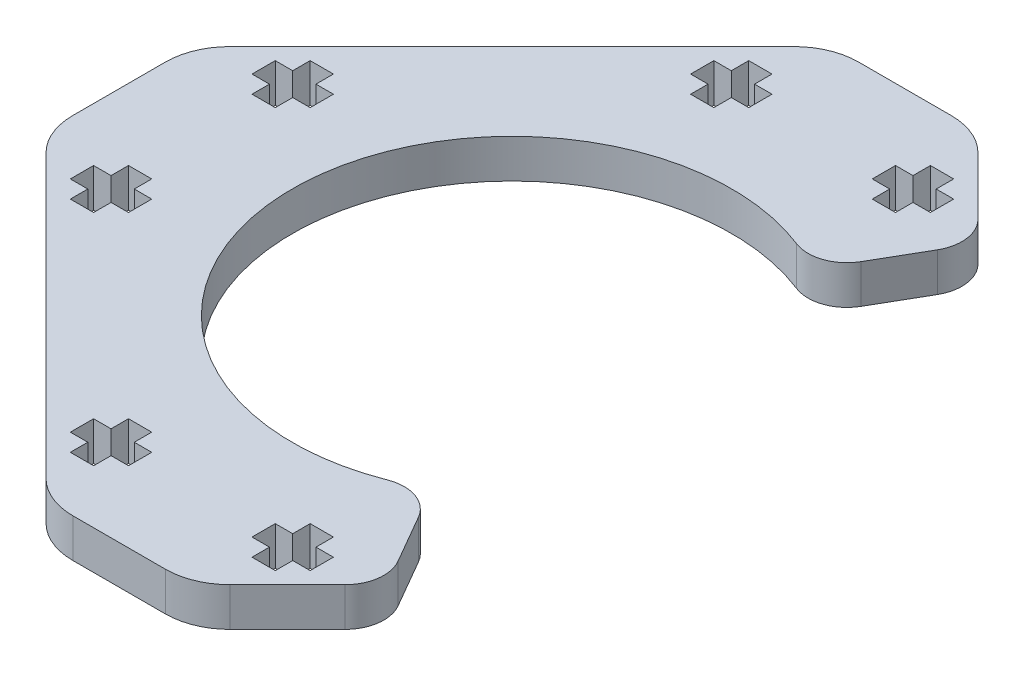
SolidWorks part; units mm, degrees
ref_plane "Front Plane" through (0, 0, 0) normal (0, 0, 1) x (1, 0, 0)
ref_plane "Top Plane" through (0, 0, 0) normal (0, 1, 0) x (1, 0, 0)
ref_plane "Right Plane" through (0, 0, 0) normal (1, 0, 0) x (0, 0, -1)
sketch "Sketch1" plane through (0, 0, 0) normal (0, 1, 0) x (1, 0, 0)
  line L0 (17.5699, 22.8627) -> (11.4915, 28.9411)
  line L1 (7.956, 30.4056) -> (0.7844, 30.4056)
  line L2 (-2.7512, 28.9411) -> (-24.571, 7.1213)
  line L3 (-26.0354, 3.5858) -> (-26.0354, -3.5858)
  line L4 (-24.571, -7.1213) -> (-2.7512, -28.9411)
  line L5 (0.7844, -30.4056) -> (7.956, -30.4056)
  line L6 (11.4915, -28.9411) -> (17.5699, -22.8627)
  line L11 (-11.5989, 5.83) -> (4.3702, 0) construction
  line L12 (-11.5989, -5.83) -> (4.3702, 0) construction
  line L13 (-3.7616, 22.2739) -> (4.3702, 0) construction
  line L14 (12.8702, 14.7224) -> (17.5699, 22.8627)
  line L15 (12.8702, -14.7224) -> (17.5699, -22.8627)
  arc A7 (11.4915, 28.9411) -> (7.956, 30.4056) centre (7.956, 25.4056) ccw
  arc A8 (0.7844, 30.4056) -> (-2.7512, 28.9411) centre (0.7844, 25.4056) ccw
  arc A9 (-24.571, 7.1213) -> (-26.0354, 3.5858) centre (-21.0354, 3.5858) ccw
  arc A10 (-26.0354, -3.5858) -> (-24.571, -7.1213) centre (-21.0354, -3.5858) ccw
  arc A11 (-2.7512, -28.9411) -> (0.7844, -30.4056) centre (0.7844, -25.4056) ccw
  arc A12 (7.956, -30.4056) -> (11.4915, -28.9411) centre (7.956, -25.4056) ccw
  arc A16 (12.8702, 14.7224) -> (12.8702, -14.7224) centre (4.3702, 0) ccw
  dimension "D1" = 51
  dimension "D2" = 17
extrude "Boss-Extrude1" add sketch "Sketch1" along normal blind 3
sketch "Sketch2" plane through (0, 3, 0) normal (0, 1, 0) x (1, 0, 0)
  line L12 (-21.8798, 7.9294) -> (-21.8798, 6.1294)
  line L13 (-21.8798, 6.1294) -> (-20.5298, 6.1294)
  line L14 (-20.5298, 6.1294) -> (-20.5298, 4.7794)
  line L15 (-20.5298, 4.7794) -> (-18.7298, 4.7794)
  line L16 (-18.7298, 4.7794) -> (-18.7298, 6.1294)
  line L17 (-18.7298, 6.1294) -> (-17.3798, 6.1294)
  line L18 (-17.3798, 6.1294) -> (-17.3798, 7.9294)
  line L19 (-17.3798, 7.9294) -> (-18.7298, 7.9294)
  line L20 (-18.7298, 7.9294) -> (-18.7298, 9.2794)
  line L21 (-18.7298, 9.2794) -> (-20.5298, 9.2794)
  line L22 (-20.5298, 9.2794) -> (-20.5298, 7.9294)
  line L23 (-20.5298, 7.9294) -> (-21.8798, 7.9294)
  line L24 (-21.8798, 7.9294) -> (-21.8798, 6.1294)
  line L25 (-21.8798, 6.1294) -> (-20.5298, 6.1294)
  line L26 (-20.5298, 6.1294) -> (-20.5298, 4.7794)
  line L27 (-20.5298, 4.7794) -> (-18.7298, 4.7794)
  line L28 (-18.7298, 4.7794) -> (-18.7298, 6.1294)
  line L29 (-18.7298, 6.1294) -> (-17.3798, 6.1294)
  line L30 (-17.3798, 6.1294) -> (-17.3798, 7.9294)
  line L31 (-17.3798, 7.9294) -> (-18.7298, 7.9294)
  line L32 (-18.7298, 7.9294) -> (-18.7298, 9.2794)
  line L33 (-18.7298, 9.2794) -> (-20.5298, 9.2794)
  line L34 (-20.5298, 9.2794) -> (-20.5298, 7.9294)
  line L35 (-20.5298, 7.9294) -> (-21.8798, 7.9294)
  line L36 (-18.7298, -4.7794) -> (-20.5298, -4.7794)
  line L37 (-20.5298, -4.7794) -> (-20.5298, -6.1294)
  line L38 (-20.5298, -6.1294) -> (-21.8798, -6.1294)
  line L39 (-21.8798, -6.1294) -> (-21.8798, -7.9294)
  line L40 (-21.8798, -7.9294) -> (-20.5298, -7.9294)
  line L41 (-20.5298, -7.9294) -> (-20.5298, -9.2794)
  line L42 (-20.5298, -9.2794) -> (-18.7298, -9.2794)
  line L43 (-18.7298, -9.2794) -> (-18.7298, -7.9294)
  line L44 (-18.7298, -7.9294) -> (-17.3798, -7.9294)
  line L45 (-17.3798, -7.9294) -> (-17.3798, -6.1294)
  line L46 (-17.3798, -6.1294) -> (-18.7298, -6.1294)
  line L47 (-18.7298, -6.1294) -> (-18.7298, -4.7794)
  line L48 (-18.7298, -4.7794) -> (-20.5298, -4.7794)
  line L49 (-20.5298, -4.7794) -> (-20.5298, -6.1294)
  line L50 (-20.5298, -6.1294) -> (-21.8798, -6.1294)
  line L51 (-21.8798, -6.1294) -> (-21.8798, -7.9294)
  line L52 (-21.8798, -7.9294) -> (-20.5298, -7.9294)
  line L53 (-20.5298, -7.9294) -> (-20.5298, -9.2794)
  line L54 (-20.5298, -9.2794) -> (-18.7298, -9.2794)
  line L55 (-18.7298, -9.2794) -> (-18.7298, -7.9294)
  line L56 (-18.7298, -7.9294) -> (-17.3798, -7.9294)
  line L57 (-17.3798, -7.9294) -> (-17.3798, -6.1294)
  line L58 (-17.3798, -6.1294) -> (-18.7298, -6.1294)
  line L59 (-18.7298, -6.1294) -> (-18.7298, -4.7794)
  line L60 (12.2996, 23.1) -> (13.6496, 23.1)
  line L61 (13.6496, 23.1) -> (13.6496, 24.9)
  line L62 (13.6496, 24.9) -> (12.2996, 24.9)
  line L63 (12.2996, 24.9) -> (12.2996, 26.25)
  line L64 (12.2996, 26.25) -> (10.4996, 26.25)
  line L65 (10.4996, 26.25) -> (10.4996, 24.9)
  line L66 (10.4996, 24.9) -> (9.1496, 24.9)
  line L67 (9.1496, 24.9) -> (9.1496, 23.1)
  line L68 (9.1496, 23.1) -> (10.4996, 23.1)
  line L69 (10.4996, 23.1) -> (10.4996, 21.75)
  line L70 (10.4996, 21.75) -> (12.2996, 21.75)
  line L71 (12.2996, 21.75) -> (12.2996, 23.1)
  line L72 (12.2996, 23.1) -> (13.6496, 23.1)
  line L73 (13.6496, 23.1) -> (13.6496, 24.9)
  line L74 (13.6496, 24.9) -> (12.2996, 24.9)
  line L75 (12.2996, 24.9) -> (12.2996, 26.25)
  line L76 (12.2996, 26.25) -> (10.4996, 26.25)
  line L77 (10.4996, 26.25) -> (10.4996, 24.9)
  line L78 (10.4996, 24.9) -> (9.1496, 24.9)
  line L79 (9.1496, 24.9) -> (9.1496, 23.1)
  line L80 (9.1496, 23.1) -> (10.4996, 23.1)
  line L81 (10.4996, 23.1) -> (10.4996, 21.75)
  line L82 (10.4996, 21.75) -> (12.2996, 21.75)
  line L83 (12.2996, 21.75) -> (12.2996, 23.1)
  line L84 (30.6202, -7.9294) -> (30.6202, -6.1294)
  line L85 (30.6202, -6.1294) -> (29.2702, -6.1294)
  line L86 (29.2702, -6.1294) -> (29.2702, -4.7794)
  line L87 (29.2702, -4.7794) -> (27.4702, -4.7794)
  line L88 (27.4702, -4.7794) -> (27.4702, -6.1294)
  line L89 (27.4702, -6.1294) -> (26.1202, -6.1294)
  line L90 (26.1202, -6.1294) -> (26.1202, -7.9294)
  line L91 (26.1202, -7.9294) -> (27.4702, -7.9294)
  line L92 (27.4702, -7.9294) -> (27.4702, -9.2794)
  line L93 (27.4702, -9.2794) -> (29.2702, -9.2794)
  line L94 (29.2702, -9.2794) -> (29.2702, -7.9294)
  line L95 (29.2702, -7.9294) -> (30.6202, -7.9294)
  line L96 (30.6202, -7.9294) -> (30.6202, -6.1294)
  line L97 (30.6202, -6.1294) -> (29.2702, -6.1294)
  line L98 (29.2702, -6.1294) -> (29.2702, -4.7794)
  line L99 (29.2702, -4.7794) -> (27.4702, -4.7794)
  line L100 (27.4702, -4.7794) -> (27.4702, -6.1294)
  line L101 (27.4702, -6.1294) -> (26.1202, -6.1294)
  line L102 (26.1202, -6.1294) -> (26.1202, -7.9294)
  line L103 (26.1202, -7.9294) -> (27.4702, -7.9294)
  line L104 (27.4702, -7.9294) -> (27.4702, -9.2794)
  line L105 (27.4702, -9.2794) -> (29.2702, -9.2794)
  line L106 (29.2702, -9.2794) -> (29.2702, -7.9294)
  line L107 (29.2702, -7.9294) -> (30.6202, -7.9294)
  line L108 (-0.4093, 24.9) -> (-1.7593, 24.9)
  line L109 (-1.7593, 24.9) -> (-1.7593, 26.25)
  line L110 (-1.7593, 26.25) -> (-3.5593, 26.25)
  line L111 (-3.5593, 26.25) -> (-3.5593, 24.9)
  line L112 (-3.5593, 24.9) -> (-4.9093, 24.9)
  line L113 (-4.9093, 24.9) -> (-4.9093, 23.1)
  line L114 (-4.9093, 23.1) -> (-3.5593, 23.1)
  line L115 (-3.5593, 23.1) -> (-3.5593, 21.75)
  line L116 (-3.5593, 21.75) -> (-1.7593, 21.75)
  line L117 (-1.7593, 21.75) -> (-1.7593, 23.1)
  line L118 (-1.7593, 23.1) -> (-0.4093, 23.1)
  line L119 (-0.4093, 23.1) -> (-0.4093, 24.9)
  line L120 (-0.4093, 24.9) -> (-1.7593, 24.9)
  line L121 (-1.7593, 24.9) -> (-1.7593, 26.25)
  line L122 (-1.7593, 26.25) -> (-3.5593, 26.25)
  line L123 (-3.5593, 26.25) -> (-3.5593, 24.9)
  line L124 (-3.5593, 24.9) -> (-4.9093, 24.9)
  line L125 (-4.9093, 24.9) -> (-4.9093, 23.1)
  line L126 (-4.9093, 23.1) -> (-3.5593, 23.1)
  line L127 (-3.5593, 23.1) -> (-3.5593, 21.75)
  line L128 (-3.5593, 21.75) -> (-1.7593, 21.75)
  line L129 (-1.7593, 21.75) -> (-1.7593, 23.1)
  line L130 (-1.7593, 23.1) -> (-0.4093, 23.1)
  line L131 (-0.4093, 23.1) -> (-0.4093, 24.9)
  line L132 (30.6202, 7.9294) -> (29.2702, 7.9294)
  line L133 (30.6202, 6.1294) -> (30.6202, 7.9294)
  line L134 (29.2702, 6.1294) -> (30.6202, 6.1294)
  line L135 (29.2702, 4.7794) -> (29.2702, 6.1294)
  line L136 (27.4702, 4.7794) -> (29.2702, 4.7794)
  line L137 (27.4702, 6.1294) -> (27.4702, 4.7794)
  line L138 (26.1202, 6.1294) -> (27.4702, 6.1294)
  line L139 (26.1202, 7.9294) -> (26.1202, 6.1294)
  line L140 (27.4702, 7.9294) -> (26.1202, 7.9294)
  line L141 (27.4702, 9.2794) -> (27.4702, 7.9294)
  line L142 (29.2702, 9.2794) -> (27.4702, 9.2794)
  line L143 (29.2702, 7.9294) -> (29.2702, 9.2794)
  line L144 (30.6202, 7.9294) -> (29.2702, 7.9294)
  line L145 (30.6202, 6.1294) -> (30.6202, 7.9294)
  line L146 (29.2702, 6.1294) -> (30.6202, 6.1294)
  line L147 (29.2702, 4.7794) -> (29.2702, 6.1294)
  line L148 (27.4702, 4.7794) -> (29.2702, 4.7794)
  line L149 (27.4702, 6.1294) -> (27.4702, 4.7794)
  line L150 (26.1202, 6.1294) -> (27.4702, 6.1294)
  line L151 (26.1202, 7.9294) -> (26.1202, 6.1294)
  line L152 (27.4702, 7.9294) -> (26.1202, 7.9294)
  line L153 (27.4702, 9.2794) -> (27.4702, 7.9294)
  line L154 (29.2702, 9.2794) -> (27.4702, 9.2794)
  line L155 (29.2702, 7.9294) -> (29.2702, 9.2794)
  line L156 (-1.7593, -26.25) -> (-1.7593, -24.9)
  line L157 (-1.7593, -24.9) -> (-0.4093, -24.9)
  line L158 (-0.4093, -24.9) -> (-0.4093, -23.1)
  line L159 (-0.4093, -23.1) -> (-1.7593, -23.1)
  line L160 (-1.7593, -23.1) -> (-1.7593, -21.75)
  line L161 (-1.7593, -21.75) -> (-3.5593, -21.75)
  line L162 (-3.5593, -21.75) -> (-3.5593, -23.1)
  line L163 (-3.5593, -23.1) -> (-4.9093, -23.1)
  line L164 (-4.9093, -23.1) -> (-4.9093, -24.9)
  line L165 (-4.9093, -24.9) -> (-3.5593, -24.9)
  line L166 (-3.5593, -24.9) -> (-3.5593, -26.25)
  line L167 (-3.5593, -26.25) -> (-1.7593, -26.25)
  line L168 (-1.7593, -26.25) -> (-1.7593, -24.9)
  line L169 (-1.7593, -24.9) -> (-0.4093, -24.9)
  line L170 (-0.4093, -24.9) -> (-0.4093, -23.1)
  line L171 (-0.4093, -23.1) -> (-1.7593, -23.1)
  line L172 (-1.7593, -23.1) -> (-1.7593, -21.75)
  line L173 (-1.7593, -21.75) -> (-3.5593, -21.75)
  line L174 (-3.5593, -21.75) -> (-3.5593, -23.1)
  line L175 (-3.5593, -23.1) -> (-4.9093, -23.1)
  line L176 (-4.9093, -23.1) -> (-4.9093, -24.9)
  line L177 (-4.9093, -24.9) -> (-3.5593, -24.9)
  line L178 (-3.5593, -24.9) -> (-3.5593, -26.25)
  line L179 (-3.5593, -26.25) -> (-1.7593, -26.25)
  line L180 (12.2996, -26.25) -> (12.2996, -24.9)
  line L181 (12.2996, -24.9) -> (13.6496, -24.9)
  line L182 (13.6496, -24.9) -> (13.6496, -23.1)
  line L183 (13.6496, -23.1) -> (12.2996, -23.1)
  line L184 (12.2996, -23.1) -> (12.2996, -21.75)
  line L185 (12.2996, -21.75) -> (10.4996, -21.75)
  line L186 (10.4996, -21.75) -> (10.4996, -23.1)
  line L187 (10.4996, -23.1) -> (9.1496, -23.1)
  line L188 (9.1496, -23.1) -> (9.1496, -24.9)
  line L189 (9.1496, -24.9) -> (10.4996, -24.9)
  line L190 (10.4996, -24.9) -> (10.4996, -26.25)
  line L191 (10.4996, -26.25) -> (12.2996, -26.25)
  line L192 (12.2996, -26.25) -> (12.2996, -24.9)
  line L193 (12.2996, -24.9) -> (13.6496, -24.9)
  line L194 (13.6496, -24.9) -> (13.6496, -23.1)
  line L195 (13.6496, -23.1) -> (12.2996, -23.1)
  line L196 (12.2996, -23.1) -> (12.2996, -21.75)
  line L197 (12.2996, -21.75) -> (10.4996, -21.75)
  line L198 (10.4996, -21.75) -> (10.4996, -23.1)
  line L199 (10.4996, -23.1) -> (9.1496, -23.1)
  line L200 (9.1496, -23.1) -> (9.1496, -24.9)
  line L201 (9.1496, -24.9) -> (10.4996, -24.9)
  line L202 (10.4996, -24.9) -> (10.4996, -26.25)
  line L203 (10.4996, -26.25) -> (12.2996, -26.25)
  dimension "D1" = 0
  dimension "D2" = 0
  dimension "D3" = 0
  dimension "D4" = 0
  dimension "D5" = 0
  dimension "D6" = 0
  dimension "D7" = 0
  dimension "D8" = 0
extrude "Cut-Extrude1" cut sketch "Sketch2" against normal through all
fillet "Fillet1" radius 3 4 edges at (17.5699, 1.5, 22.8627) (12.8702, 1.5, 14.7224) (17.5699, 1.5, -22.8627) (12.8702, 1.5, -14.7224)
sketch "Sketch3" plane through (0, 3, 0) normal (0, 1, 0) x (1, 0, 0)
  line L9 (11.4915, -28.9411) -> (15.9422, -24.4904)
  line L10 (16.4189, -20.8691) -> (14.257, -17.1245)
  line L11 (14.257, 17.1245) -> (16.4189, 20.8691)
  line L12 (12.2996, -24.9) -> (13.6496, -24.9)
  line L13 (12.2996, -26.25) -> (12.2996, -24.9)
  line L14 (10.4996, -26.25) -> (12.2996, -26.25)
  line L15 (10.4996, -24.9) -> (10.4996, -26.25)
  line L16 (9.1496, -24.9) -> (10.4996, -24.9)
  line L17 (9.1496, -23.1) -> (9.1496, -24.9)
  line L18 (10.4996, -23.1) -> (9.1496, -23.1)
  line L19 (10.4996, -21.75) -> (10.4996, -23.1)
  line L20 (12.2996, -21.75) -> (10.4996, -21.75)
  line L21 (12.2996, -23.1) -> (12.2996, -21.75)
  line L22 (13.6496, -23.1) -> (12.2996, -23.1)
  line L23 (13.6496, -24.9) -> (13.6496, -23.1)
  line L24 (12.2996, -24.9) -> (13.6496, -24.9)
  line L25 (12.2996, -26.25) -> (12.2996, -24.9)
  line L26 (10.4996, -26.25) -> (12.2996, -26.25)
  line L27 (10.4996, -24.9) -> (10.4996, -26.25)
  line L28 (9.1496, -24.9) -> (10.4996, -24.9)
  line L29 (9.1496, -23.1) -> (9.1496, -24.9)
  line L30 (10.4996, -23.1) -> (9.1496, -23.1)
  line L31 (10.4996, -21.75) -> (10.4996, -23.1)
  line L32 (12.2996, -21.75) -> (10.4996, -21.75)
  line L33 (12.2996, -23.1) -> (12.2996, -21.75)
  line L34 (13.6496, -23.1) -> (12.2996, -23.1)
  line L35 (13.6496, -24.9) -> (13.6496, -23.1)
  line L36 (-1.7593, 24.9) -> (-1.7593, 26.25)
  line L37 (-0.4093, 24.9) -> (-1.7593, 24.9)
  line L38 (-0.4093, 23.1) -> (-0.4093, 24.9)
  line L39 (-1.7593, 23.1) -> (-0.4093, 23.1)
  line L40 (-1.7593, 21.75) -> (-1.7593, 23.1)
  line L41 (-3.5593, 21.75) -> (-1.7593, 21.75)
  line L42 (-3.5593, 23.1) -> (-3.5593, 21.75)
  line L43 (-4.9093, 23.1) -> (-3.5593, 23.1)
  line L44 (-4.9093, 24.9) -> (-4.9093, 23.1)
  line L45 (-3.5593, 24.9) -> (-4.9093, 24.9)
  line L46 (-3.5593, 26.25) -> (-3.5593, 24.9)
  line L47 (-1.7593, 26.25) -> (-3.5593, 26.25)
  line L48 (-1.7593, 24.9) -> (-1.7593, 26.25)
  line L49 (-0.4093, 24.9) -> (-1.7593, 24.9)
  line L50 (-0.4093, 23.1) -> (-0.4093, 24.9)
  line L51 (-1.7593, 23.1) -> (-0.4093, 23.1)
  line L52 (-1.7593, 21.75) -> (-1.7593, 23.1)
  line L53 (-3.5593, 21.75) -> (-1.7593, 21.75)
  line L54 (-3.5593, 23.1) -> (-3.5593, 21.75)
  line L55 (-4.9093, 23.1) -> (-3.5593, 23.1)
  line L56 (-4.9093, 24.9) -> (-4.9093, 23.1)
  line L57 (-3.5593, 24.9) -> (-4.9093, 24.9)
  line L58 (-3.5593, 26.25) -> (-3.5593, 24.9)
  line L59 (-1.7593, 26.25) -> (-3.5593, 26.25)
  line L60 (12.2996, 21.75) -> (12.2996, 23.1)
  line L61 (10.4996, 21.75) -> (12.2996, 21.75)
  line L62 (10.4996, 23.1) -> (10.4996, 21.75)
  line L63 (9.1496, 23.1) -> (10.4996, 23.1)
  line L64 (9.1496, 24.9) -> (9.1496, 23.1)
  line L65 (10.4996, 24.9) -> (9.1496, 24.9)
  line L66 (10.4996, 26.25) -> (10.4996, 24.9)
  line L67 (12.2996, 26.25) -> (10.4996, 26.25)
  line L68 (12.2996, 24.9) -> (12.2996, 26.25)
  line L69 (13.6496, 24.9) -> (12.2996, 24.9)
  line L70 (13.6496, 23.1) -> (13.6496, 24.9)
  line L71 (12.2996, 23.1) -> (13.6496, 23.1)
  line L72 (12.2996, 21.75) -> (12.2996, 23.1)
  line L73 (10.4996, 21.75) -> (12.2996, 21.75)
  line L74 (10.4996, 23.1) -> (10.4996, 21.75)
  line L75 (9.1496, 23.1) -> (10.4996, 23.1)
  line L76 (9.1496, 24.9) -> (9.1496, 23.1)
  line L77 (10.4996, 24.9) -> (9.1496, 24.9)
  line L78 (10.4996, 26.25) -> (10.4996, 24.9)
  line L79 (12.2996, 26.25) -> (10.4996, 26.25)
  line L80 (12.2996, 24.9) -> (12.2996, 26.25)
  line L81 (13.6496, 24.9) -> (12.2996, 24.9)
  line L82 (13.6496, 23.1) -> (13.6496, 24.9)
  line L83 (12.2996, 23.1) -> (13.6496, 23.1)
  line L84 (-20.5298, -4.7794) -> (-20.5298, -6.1294)
  line L85 (-18.7298, -4.7794) -> (-20.5298, -4.7794)
  line L86 (-18.7298, -6.1294) -> (-18.7298, -4.7794)
  line L87 (-17.3798, -6.1294) -> (-18.7298, -6.1294)
  line L88 (-17.3798, -7.9294) -> (-17.3798, -6.1294)
  line L89 (-18.7298, -7.9294) -> (-17.3798, -7.9294)
  line L90 (-18.7298, -9.2794) -> (-18.7298, -7.9294)
  line L91 (-20.5298, -9.2794) -> (-18.7298, -9.2794)
  line L92 (-20.5298, -7.9294) -> (-20.5298, -9.2794)
  line L93 (-21.8798, -7.9294) -> (-20.5298, -7.9294)
  line L94 (-21.8798, -6.1294) -> (-21.8798, -7.9294)
  line L95 (-20.5298, -6.1294) -> (-21.8798, -6.1294)
  line L96 (-20.5298, -4.7794) -> (-20.5298, -6.1294)
  line L97 (-18.7298, -4.7794) -> (-20.5298, -4.7794)
  line L98 (-18.7298, -6.1294) -> (-18.7298, -4.7794)
  line L99 (-17.3798, -6.1294) -> (-18.7298, -6.1294)
  line L100 (-17.3798, -7.9294) -> (-17.3798, -6.1294)
  line L101 (-18.7298, -7.9294) -> (-17.3798, -7.9294)
  line L102 (-18.7298, -9.2794) -> (-18.7298, -7.9294)
  line L103 (-20.5298, -9.2794) -> (-18.7298, -9.2794)
  line L104 (-20.5298, -7.9294) -> (-20.5298, -9.2794)
  line L105 (-21.8798, -7.9294) -> (-20.5298, -7.9294)
  line L106 (-21.8798, -6.1294) -> (-21.8798, -7.9294)
  line L107 (-20.5298, -6.1294) -> (-21.8798, -6.1294)
  line L108 (-20.5298, 7.9294) -> (-21.8798, 7.9294)
  line L109 (-20.5298, 9.2794) -> (-20.5298, 7.9294)
  line L110 (-18.7298, 9.2794) -> (-20.5298, 9.2794)
  line L111 (-18.7298, 7.9294) -> (-18.7298, 9.2794)
  line L112 (-17.3798, 7.9294) -> (-18.7298, 7.9294)
  line L113 (-17.3798, 6.1294) -> (-17.3798, 7.9294)
  line L114 (-18.7298, 6.1294) -> (-17.3798, 6.1294)
  line L115 (-18.7298, 4.7794) -> (-18.7298, 6.1294)
  line L116 (-20.5298, 4.7794) -> (-18.7298, 4.7794)
  line L117 (-20.5298, 6.1294) -> (-20.5298, 4.7794)
  line L118 (-21.8798, 6.1294) -> (-20.5298, 6.1294)
  line L119 (-21.8798, 7.9294) -> (-21.8798, 6.1294)
  line L120 (-20.5298, 7.9294) -> (-21.8798, 7.9294)
  line L121 (-20.5298, 9.2794) -> (-20.5298, 7.9294)
  line L122 (-18.7298, 9.2794) -> (-20.5298, 9.2794)
  line L123 (-18.7298, 7.9294) -> (-18.7298, 9.2794)
  line L124 (-17.3798, 7.9294) -> (-18.7298, 7.9294)
  line L125 (-17.3798, 6.1294) -> (-17.3798, 7.9294)
  line L126 (-18.7298, 6.1294) -> (-17.3798, 6.1294)
  line L127 (-18.7298, 4.7794) -> (-18.7298, 6.1294)
  line L128 (-20.5298, 4.7794) -> (-18.7298, 4.7794)
  line L129 (-20.5298, 6.1294) -> (-20.5298, 4.7794)
  line L130 (-21.8798, 6.1294) -> (-20.5298, 6.1294)
  line L131 (-21.8798, 7.9294) -> (-21.8798, 6.1294)
  line L132 (-3.5593, -26.25) -> (-1.7593, -26.25)
  line L133 (-3.5593, -24.9) -> (-3.5593, -26.25)
  line L134 (-4.9093, -24.9) -> (-3.5593, -24.9)
  line L135 (-4.9093, -23.1) -> (-4.9093, -24.9)
  line L136 (-3.5593, -23.1) -> (-4.9093, -23.1)
  line L137 (-3.5593, -21.75) -> (-3.5593, -23.1)
  line L138 (-1.7593, -21.75) -> (-3.5593, -21.75)
  line L139 (-1.7593, -23.1) -> (-1.7593, -21.75)
  line L140 (-0.4093, -23.1) -> (-1.7593, -23.1)
  line L141 (-0.4093, -24.9) -> (-0.4093, -23.1)
  line L142 (-1.7593, -24.9) -> (-0.4093, -24.9)
  line L143 (-1.7593, -26.25) -> (-1.7593, -24.9)
  line L144 (-3.5593, -26.25) -> (-1.7593, -26.25)
  line L145 (-3.5593, -24.9) -> (-3.5593, -26.25)
  line L146 (-4.9093, -24.9) -> (-3.5593, -24.9)
  line L147 (-4.9093, -23.1) -> (-4.9093, -24.9)
  line L148 (-3.5593, -23.1) -> (-4.9093, -23.1)
  line L149 (-3.5593, -21.75) -> (-3.5593, -23.1)
  line L150 (-1.7593, -21.75) -> (-3.5593, -21.75)
  line L151 (-1.7593, -23.1) -> (-1.7593, -21.75)
  line L152 (-0.4093, -23.1) -> (-1.7593, -23.1)
  line L153 (-0.4093, -24.9) -> (-0.4093, -23.1)
  line L154 (-1.7593, -24.9) -> (-0.4093, -24.9)
  line L155 (-1.7593, -26.25) -> (-1.7593, -24.9)
  line L156 (15.9422, 24.4904) -> (11.4915, 28.9411)
  line L157 (7.956, 30.4056) -> (0.7844, 30.4056)
  line L158 (-2.7512, 28.9411) -> (-24.571, 7.1213)
  line L159 (-26.0354, 3.5858) -> (-26.0354, -3.5858)
  line L160 (-24.571, -7.1213) -> (-2.7512, -28.9411)
  line L161 (0.7844, -30.4056) -> (7.956, -30.4056)
  line L162 (11.4915, -28.9411) -> (15.9422, -24.4904)
  line L163 (16.4189, -20.8691) -> (14.257, -17.1245)
  line L164 (14.257, 17.1245) -> (16.4189, 20.8691)
  line L165 (15.9422, 24.4904) -> (11.4915, 28.9411)
  line L166 (7.956, 30.4056) -> (0.7844, 30.4056)
  line L167 (-2.7512, 28.9411) -> (-24.571, 7.1213)
  line L168 (-26.0354, 3.5858) -> (-26.0354, -3.5858)
  line L169 (-24.571, -7.1213) -> (-2.7512, -28.9411)
  line L170 (0.7844, -30.4056) -> (7.956, -30.4056)
  arc A11 (15.9422, -24.4904) -> (16.4189, -20.8691) centre (13.8209, -22.3691) ccw
  arc A12 (14.257, -17.1245) -> (10.5656, -15.8309) centre (11.659, -18.6245) ccw
  arc A13 (10.5656, 15.8309) -> (10.5656, -15.8309) centre (4.3702, 0) ccw
  arc A14 (10.5656, 15.8309) -> (14.257, 17.1245) centre (11.659, 18.6245) ccw
  arc A15 (16.4189, 20.8691) -> (15.9422, 24.4904) centre (13.8209, 22.3691) ccw
  arc A16 (11.4915, 28.9411) -> (7.956, 30.4056) centre (7.956, 25.4056) ccw
  arc A17 (0.7844, 30.4056) -> (-2.7512, 28.9411) centre (0.7844, 25.4056) ccw
  arc A18 (-24.571, 7.1213) -> (-26.0354, 3.5858) centre (-21.0354, 3.5858) ccw
  arc A19 (-26.0354, -3.5858) -> (-24.571, -7.1213) centre (-21.0354, -3.5858) ccw
  arc A20 (-2.7512, -28.9411) -> (0.7844, -30.4056) centre (0.7844, -25.4056) ccw
  arc A21 (7.956, -30.4056) -> (11.4915, -28.9411) centre (7.956, -25.4056) ccw
  arc A22 (15.9422, -24.4904) -> (16.4189, -20.8691) centre (13.8209, -22.3691) ccw
  arc A23 (14.257, -17.1245) -> (10.5656, -15.8309) centre (11.659, -18.6245) ccw
  arc A24 (10.5656, 15.8309) -> (10.5656, -15.8309) centre (4.3702, 0) ccw
  arc A25 (10.5656, 15.8309) -> (14.257, 17.1245) centre (11.659, 18.6245) ccw
  arc A26 (16.4189, 20.8691) -> (15.9422, 24.4904) centre (13.8209, 22.3691) ccw
  arc A27 (11.4915, 28.9411) -> (7.956, 30.4056) centre (7.956, 25.4056) ccw
  arc A28 (0.7844, 30.4056) -> (-2.7512, 28.9411) centre (0.7844, 25.4056) ccw
  arc A29 (-24.571, 7.1213) -> (-26.0354, 3.5858) centre (-21.0354, 3.5858) ccw
  arc A30 (-26.0354, -3.5858) -> (-24.571, -7.1213) centre (-21.0354, -3.5858) ccw
  arc A31 (-2.7512, -28.9411) -> (0.7844, -30.4056) centre (0.7844, -25.4056) ccw
  arc A32 (7.956, -30.4056) -> (11.4915, -28.9411) centre (7.956, -25.4056) ccw
  dimension "D1" = 0
  dimension "D2" = 0
  dimension "D3" = 0
  dimension "D4" = 0
  dimension "D5" = 0
  dimension "D6" = 0
  dimension "D7" = 0
